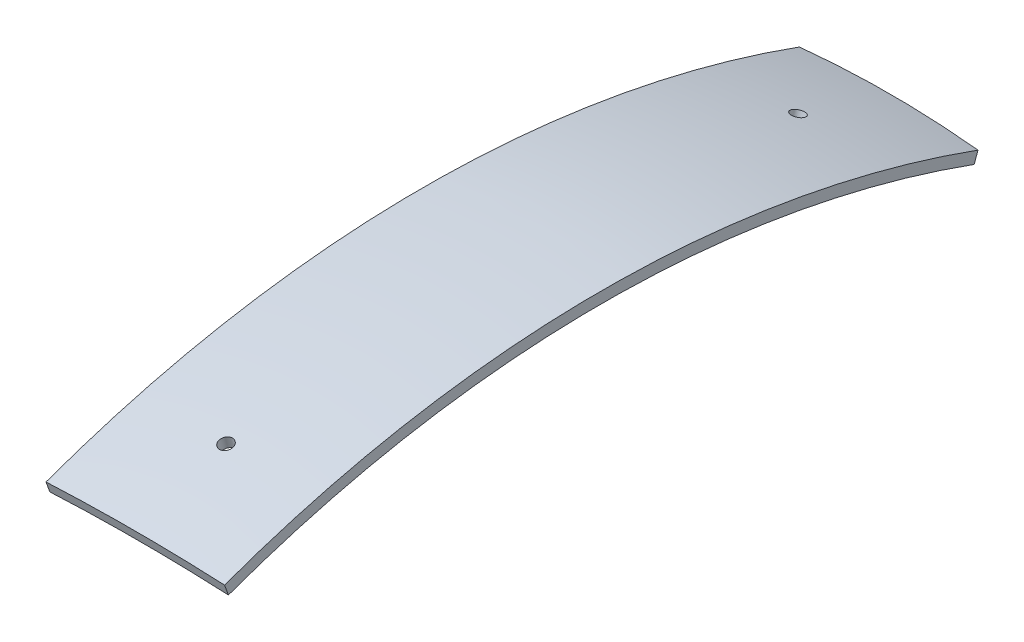
SolidWorks part; units mm, degrees
ref_plane "Front Plane" through (0, 0, 0) normal (0, 0, 1) x (1, 0, 0)
ref_plane "Top Plane" through (0, 0, 0) normal (0, 1, 0) x (1, 0, 0)
ref_plane "Right Plane" through (0, 0, 0) normal (1, 0, 0) x (0, 0, -1)
sketch "Sketch1" plane through (0, 0, 0) normal (0, 0, 1) x (1, 0, 0)
  line L0 (0, 0) -> (0, 326.4526)
  line L1 (20, 0) -> (20, 326.4526)
  line L2 (-20, 0) -> (-20, 326.4526)
  line L3 (-20, 0) -> (20, 0)
  circle A0 centre (0, 0) radius 247.5
  circle A1 centre (0, 0) radius 245
  dimension "D1" = 495
  dimension "D2" = 490
  dimension "D3" = 20
  dimension "D4" = 20
revolve "Revolve1" add sketch "Sketch1" angle 20 about L3
sketch "Sketch2" plane through (0, 0, 0) normal (0, 0, 1) x (1, 0, 0)
  line L0 (0, 0) -> (81.7913, 0)
ref_plane "Plane1" through (0, 0, 0) normal (0, -0.2588, 0.9659) x (1, 0, 0)
sketch "Sketch3" plane through (0, 0, 0) normal (0, -0.2588, 0.9659) x (1, 0, 0)
  line L0 (0, 0) -> (0, 272.8628)
  line L1 (1.5, 0) -> (1.5, 272.8628)
  line L2 (-19.6798, 218.7222) -> (33.1092, 218.7222)
  line L3 (0, 272.8628) -> (1.5, 272.8628)
  dimension "D1" = 1.5
revolve "Cut-Revolve1" cut sketch "Sketch3" angle 360 about L0
sketch "Sketch4" plane through (0, 0, 0) normal (0, 0, 1) x (1, 0, 0)
  line L0 (0, 0) -> (0, 201.3688)
pattern_circular "CirPattern2" count 2 every 180 about axis through (0, 0, 0) along (0, 1, 0) of "Cut-Revolve1"
